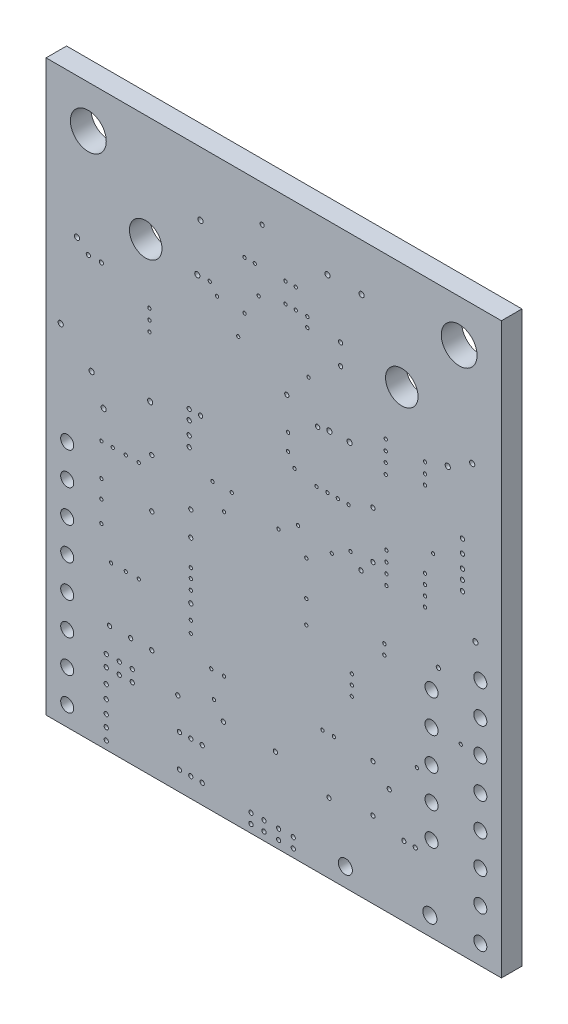
SolidWorks part; units mm, degrees
ref_plane "Front Plane" through (0, 0, 0) normal (0, 0, 1) x (1, 0, 0)
ref_plane "Top Plane" through (0, 0, 0) normal (0, 1, 0) x (1, 0, 0)
ref_plane "Right Plane" through (0, 0, 0) normal (1, 0, 0) x (0, 0, -1)
ref_plane "Dielectric_Layer Layer 1" through (0, 0, 1.6) normal (0, 0, 1) x (1, 0, 0)
sketch "Sketch1" plane through (0, 0, 0) normal (0, 0, 1) x (1, 0, 0)
  line L0 (0, 44.45) -> (0, 0)
  line L1 (0, 0) -> (35.56, 0)
  line L2 (35.56, 0) -> (35.56, 44.45)
  line L3 (35.56, 44.45) -> (0, 44.45)
extrude "Board_Outline" add sketch "Sketch1" along normal blind 1.6 separate body
sketch "Sketch2" plane through (0, 0, 0) normal (0, 0, 1) x (1, 0, 0)
  circle A0 centre (29.591, 23.622) radius 0.127
  circle A1 centre (32.385, 14.224) radius 0.127
  circle A2 centre (20.32, 18.034) radius 0.127
  circle A3 centre (13.111, 7.6) radius 0.127
  circle A4 centre (18.7, 37.15) radius 0.127
  circle A5 centre (19.676, 22.67) radius 0.127
  circle A6 centre (16.3, 38.7) radius 0.127
  circle A7 centre (18.149, 21.651) radius 0.127
  circle A8 centre (18.7, 38.7) radius 0.127
  circle A9 centre (20.322, 20.778) radius 0.127
  circle A10 centre (12.78, 35.731) radius 0.127
  circle A11 centre (19.5, 37.15) radius 0.127
  circle A12 centre (13, 22.3) radius 0.127
  circle A13 centre (13.35, 35) radius 0.127
  circle A14 centre (20.4, 37.15) radius 0.127
  circle A15 centre (18.9, 28.573) radius 0.127
  circle A16 centre (15.5, 38.7) radius 0.127
  circle A17 centre (14.5, 22.3) radius 0.127
  circle A18 centre (19.5, 38.7) radius 0.127
  circle A19 centre (13.9, 20.7) radius 0.127
  circle A20 centre (15.5, 34.925) radius 0.127
  circle A21 centre (12.899, 9.58) radius 0.127
  circle A22 centre (16.6, 36.65) radius 0.127
  circle A23 centre (13.899, 9.58) radius 0.127
  circle A24 centre (20.4, 36.4) radius 0.127
  circle A25 centre (18.9, 27.273) radius 0.127
  circle A26 centre (22.311, 22.097) radius 0.127
  circle A27 centre (20.5, 33.1) radius 0.127
  circle A28 centre (19.399, 26.384) radius 0.127
  circle A29 centre (4.318, 20.701) radius 0.127
  circle A30 centre (4.318, 16.764) radius 0.127
  circle A31 centre (5.08, 12.827) radius 0.127
  circle A32 centre (31.369, 32.512) radius 0.2032
  circle A33 centre (8.255, 21.717) radius 0.1651
  circle A34 centre (5.207, 20.701) radius 0.127
  circle A35 centre (7.239, 12.827) radius 0.127
  circle A36 centre (30.634, 18.515) radius 0.1651
  circle A37 centre (24.592, 22.079) radius 0.1651
  circle A38 centre (33.528, 21.717) radius 0.2032
  circle A39 centre (4.318, 18.161) radius 0.127
  circle A40 centre (4.318, 15.113) radius 0.127
  circle A41 centre (17.018, 0.635) radius 0.1651
  circle A42 centre (16.002, 0.635) radius 0.1651
  circle A43 centre (32.512, 24.638) radius 0.1651
  circle A44 centre (32.512, 25.4) radius 0.1651
  circle A45 centre (28.829, 5.461) radius 0.1651
  circle A46 centre (27.94, 5.461) radius 0.1651
  circle A47 centre (16.002, 1.397) radius 0.1651
  circle A48 centre (17.018, 1.397) radius 0.1651
  circle A49 centre (4.699, 0.635) radius 0.1651
  circle A50 centre (4.699, 1.524) radius 0.1651
  circle A51 centre (4.699, 2.413) radius 0.1651
  circle A52 centre (6.223, 12.827) radius 0.127
  circle A53 centre (7.239, 20.701) radius 0.127
  circle A54 centre (11.303, 17.653) radius 0.1651
  circle A55 centre (6.223, 20.701) radius 0.127
  circle A56 centre (11.176, 26.289) radius 0.1651
  circle A57 centre (12.065, 26.289) radius 0.1651
  circle A58 centre (6.604, 8.509) radius 0.1651
  circle A59 centre (8.255, 8.509) radius 0.1651
  circle A60 centre (10.287, 6.477) radius 0.1651
  circle A61 centre (17.907, 6.477) radius 0.1651
  circle A62 centre (1.143, 27.051) radius 0.2032
  circle A63 centre (4.4958, 22.987) radius 0.2032
  circle A64 centre (25.527, 26.797) radius 0.1651
  circle A65 centre (25.527, 5.969) radius 0.1651
  circle A66 centre (32.512, 26.162) radius 0.1651
  circle A67 centre (12.192, 4.064) radius 0.1651
  circle A68 centre (12.192, 1.524) radius 0.1651
  circle A69 centre (10.414, 1.524) radius 0.1651
  circle A70 centre (10.414, 4.064) radius 0.1651
  circle A71 centre (11.303, 4.064) radius 0.1651
  circle A72 centre (11.303, 1.524) radius 0.1651
  circle A73 centre (16.873, 41.6) radius 0.1651
  circle A74 centre (23, 35.1) radius 0.1651
  circle A75 centre (22.127, 30.273) radius 0.2032
  circle A76 centre (18.8, 31.0635) radius 0.1651
  circle A77 centre (11.303, 13.208) radius 0.1651
  circle A78 centre (26.5746, 23.641) radius 0.127
  circle A79 centre (21.209, 30.099) radius 0.1651
  circle A80 centre (11.176, 25.527) radius 0.1651
  circle A81 centre (24.638, 40.767) radius 0.2032
  circle A82 centre (11.811, 35.687) radius 0.2032
  circle A83 centre (21.59, 9.779) radius 0.127
  circle A84 centre (22.479, 9.779) radius 0.127
  circle A85 centre (11.303, 14.097) radius 0.127
  circle A86 centre (8.071, 29.953) radius 0.127
  circle A87 centre (11.303, 14.883) radius 0.127
  circle A88 centre (8.071, 30.753) radius 0.127
  circle A89 centre (11.303, 15.621) radius 0.127
  circle A90 centre (8.071, 31.553) radius 0.127
  circle A91 centre (23, 36.7) radius 0.1651
  circle A92 centre (3.556, 25.019) radius 0.2032
  circle A93 centre (2.413, 33.528) radius 0.2032
  circle A94 centre (20.32, 16.256) radius 0.127
  circle A95 centre (29.591, 24.384) radius 0.127
  circle A96 centre (19.304, 0.635) radius 0.1651
  circle A97 centre (19.304, 1.397) radius 0.1651
  circle A98 centre (18.161, 1.397) radius 0.1651
  circle A99 centre (18.161, 0.635) radius 0.1651
  circle A100 centre (30.226, 26.035) radius 0.127
  circle A101 centre (21.117, 26.019) radius 0.127
  circle A102 centre (29.591, 22.86) radius 0.127
  circle A103 centre (26.416, 17.272) radius 0.127
  circle A104 centre (29.591, 22.098) radius 0.127
  circle A105 centre (26.416, 18.034) radius 0.127
  circle A106 centre (22.7838, 26.035) radius 0.127
  circle A107 centre (29.591, 31.115) radius 0.127
  circle A108 centre (21.971, 26.035) radius 0.127
  circle A109 centre (29.591, 30.353) radius 0.127
  circle A110 centre (29.591, 31.9278) radius 0.127
  circle A111 centre (23.622, 26.035) radius 0.127
  circle A112 centre (11.303, 11.176) radius 0.127
  circle A113 centre (11.303, 12.065) radius 0.127
  circle A114 centre (23.78, 22.956) radius 0.127
  circle A115 centre (23.876, 13.208) radius 0.127
  circle A116 centre (23.876, 13.97) radius 0.127
  circle A117 centre (28.956, 10.922) radius 0.127
  circle A118 centre (23.876, 14.732) radius 0.127
  circle A119 centre (22.098, 5.461) radius 0.1651
  circle A120 centre (26.797, 8.382) radius 0.1651
  circle A121 centre (11.303, 19.558) radius 0.1651
  circle A122 centre (25.527, 23.114) radius 0.1651
  circle A123 centre (32.512, 27.178) radius 0.1651
  circle A124 centre (32.512, 28.194) radius 0.1651
  circle A125 centre (5.715, 6.477) radius 0.1651
  circle A126 centre (4.699, 6.477) radius 0.1651
  circle A127 centre (6.731, 6.477) radius 0.1651
  circle A128 centre (11.176, 24.511) radius 0.1651
  circle A129 centre (8.255, 17.907) radius 0.1651
  circle A130 centre (4.318, 32.766) radius 0.1651
  circle A131 centre (11.176, 23.711) radius 0.1651
  circle A132 centre (6.731, 5.588) radius 0.1651
  circle A133 centre (5.715, 5.588) radius 0.1651
  circle A134 centre (4.953, 8.509) radius 0.1651
  circle A135 centre (13.843, 6.477) radius 0.1651
  circle A136 centre (25.527, 9.652) radius 0.1651
  circle A137 centre (4.699, 3.429) radius 0.1651
  circle A138 centre (4.699, 4.445) radius 0.1651
  circle A139 centre (4.699, 5.588) radius 0.1651
  circle A140 centre (3.302, 32.766) radius 0.1651
  circle A141 centre (15, 33.1) radius 0.127
  circle A142 centre (26.5746, 22.041) radius 0.127
  circle A143 centre (26.5746, 22.841) radius 0.127
  circle A144 centre (26.5746, 24.441) radius 0.127
  circle A145 centre (26.524, 31.934) radius 0.127
  circle A146 centre (26.524, 31.134) radius 0.127
  circle A147 centre (26.524, 30.334) radius 0.127
  circle A148 centre (26.524, 29.534) radius 0.127
  circle A149 centre (33.274, 33.655) radius 0.2032
  circle A150 centre (23.7, 30.304) radius 0.2032
  circle A151 centre (21.971, 40.767) radius 0.2032
  circle A152 centre (8.128, 25.273) radius 0.2032
  circle A153 centre (12.065, 39.497) radius 0.2032
extrude "NPTH" cut sketch "Sketch2" along normal through all
sketch "Sketch3" plane through (0, 0, 0) normal (0, 0, 1) x (1, 0, 0)
  circle A0 centre (3.3, 41.15) radius 1.4
  circle A1 centre (32.26, 41.15) radius 1.4
  circle A2 centre (33.91, 19.3) radius 0.51
  circle A3 centre (33.91, 16.76) radius 0.51
  circle A4 centre (33.91, 14.22) radius 0.51
  circle A5 centre (33.91, 11.68) radius 0.51
  circle A6 centre (33.91, 9.14) radius 0.51
  circle A7 centre (33.91, 6.6) radius 0.51
  circle A8 centre (33.91, 4.06) radius 0.51
  circle A9 centre (33.91, 1.52) radius 0.51
  circle A10 centre (1.65, 19.3) radius 0.51
  circle A11 centre (1.65, 16.76) radius 0.51
  circle A12 centre (1.65, 14.22) radius 0.51
  circle A13 centre (1.65, 11.68) radius 0.51
  circle A14 centre (1.65, 9.14) radius 0.51
  circle A15 centre (1.65, 6.6) radius 0.51
  circle A16 centre (1.65, 4.06) radius 0.51
  circle A17 centre (1.65, 1.52) radius 0.51
  circle A18 centre (30.1, 16.76) radius 0.51
  circle A19 centre (30.1, 14.22) radius 0.51
  circle A20 centre (30.1, 11.68) radius 0.51
  circle A21 centre (30.1, 9.14) radius 0.51
  circle A22 centre (30.1, 6.6) radius 0.51
  circle A23 centre (7.78, 36.07) radius 1.27
  circle A24 centre (27.78, 36.07) radius 1.27
  circle A25 centre (23.37, 1.45) radius 0.55
  circle A26 centre (29.97, 1.45) radius 0.55
extrude "PTH" cut sketch "Sketch3" along normal through all
